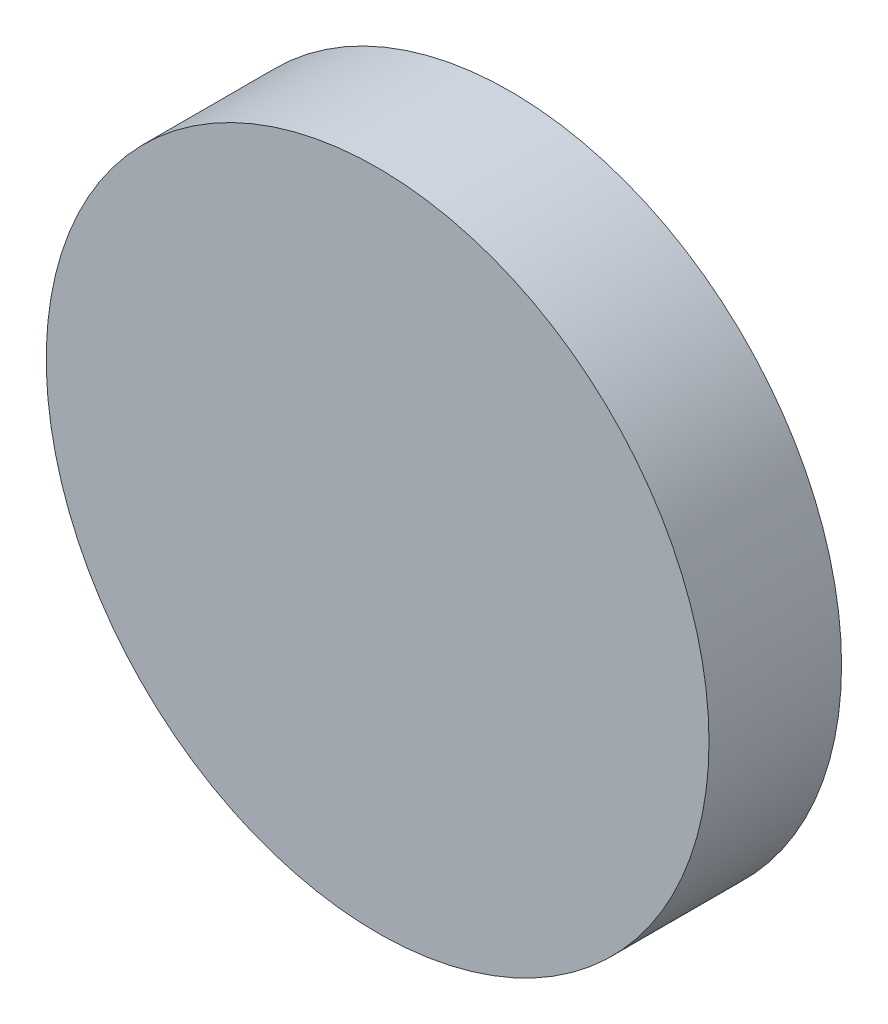
SolidWorks part; units mm, degrees
ref_plane "前视基准面" through (0, 0, 0) normal (0, 0, 1) x (1, 0, 0)
ref_plane "上视基准面" through (0, 0, 0) normal (0, 1, 0) x (1, 0, 0)
ref_plane "右视基准面" through (0, 0, 0) normal (1, 0, 0) x (0, 0, -1)
sketch "草图1" plane through (0, 0, 0) normal (0, 0, 1) x (1, 0, 0)
  circle A0 centre (0, 0) radius 15
  dimension "D1" = 30
extrude "凸台-拉伸1" add sketch "草图1" along normal blind 6 contours A0
